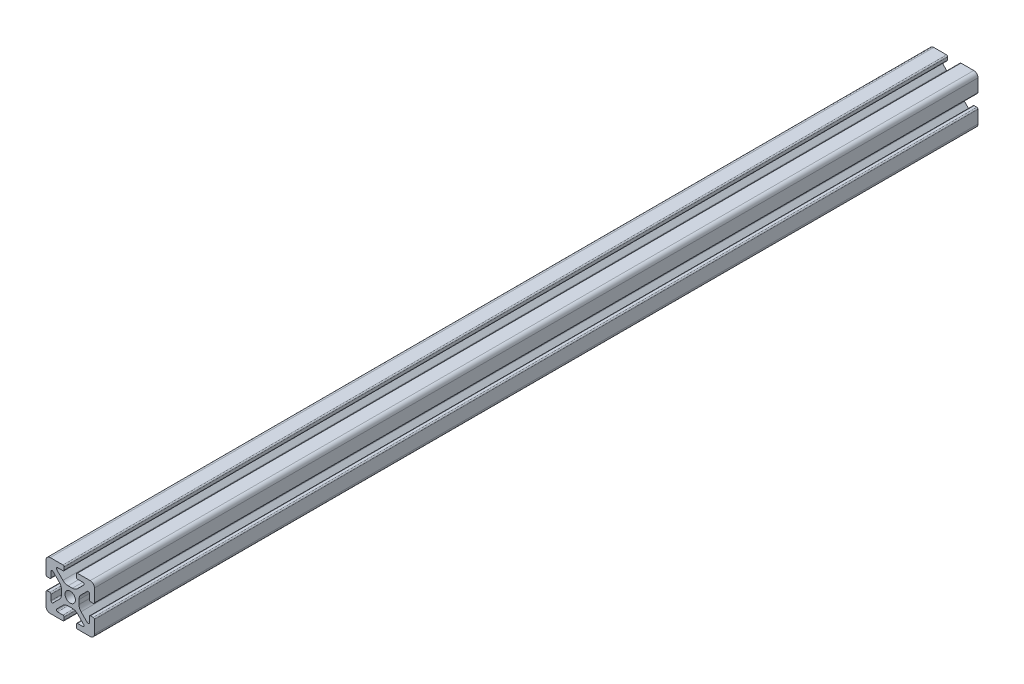
SolidWorks part; units mm, degrees
ref_plane "Front Plane" through (0, 0, 0) normal (0, 0, 1) x (1, 0, 0)
ref_plane "Top Plane" through (0, 0, 0) normal (0, 1, 0) x (1, 0, 0)
ref_plane "Right Plane" through (0, 0, 0) normal (1, 0, 0) x (0, 0, -1)
sketch "Sketch2" plane through (0, 0, 0) normal (0, 0, 1) x (1, 0, 0)
  line L0 (0, 10) -> (0, -10) construction
  line L1 (-10, 0) -> (10, 0) construction
  line L2 (2.5, -10) -> (10, -10)
  line L3 (10, -10) -> (10, -2.5)
  line L4 (2.5, -10) -> (2.5, -7.9246)
  line L5 (2.5, -7.9246) -> (6.4571, -7.9246)
  line L6 (6.4571, -7.9246) -> (2.1325, -3.6)
  line L7 (0, 0) -> (10, -10) construction
  line L8 (10, -2.5) -> (7.9246, -2.5)
  line L9 (7.9246, -2.5) -> (7.9246, -6.4571)
  line L10 (7.9246, -6.4571) -> (3.6, -2.1325)
  line L11 (5.7623, -4.2948) -> (4.2948, -5.7623) construction
  circle A0 centre (0, 0) radius 2.15
  arc A1 (5.25, -7.9246) -> (5.6036, -7.0711) centre (5.25, -7.4246) ccw construction
  point P8 (0, -3.6)
  point P16 (5.0286, -5.0286)
  dimension "Center Hole Diameter" = 4.3
  dimension "D3" = 0.5
  dimension "Rail Height" = 20
  dimension "Rail Width" = 20
  dimension "T-Slot Width" = 5
  dimension "Slot Depth" = 6.4
  dimension "Slot Inner Width" = 11.5
sketch "Sketch3" plane through (0, 0, 0) normal (1, 0, 0) x (0, 0, -1)
  line L0 (-182.5, -10) -> (182.5, -10) construction
  line L1 (-157.1, 0) -> (157.1, 0) construction
  dimension "Length" = 365
  dimension "D1" = 25.4
sketch "Sketch4" plane through (0, 0, 0) normal (0, 0, 1) x (1, 0, 0)
  line L0 (3, -10) -> (8.25, -10)
  line L1 (2.5, -10) -> (10, -10) construction
  line L2 (2.5, -10) -> (2.5, -7.9246) construction
  line L3 (2.5, -7.9246) -> (6.4571, -7.9246) construction
  line L4 (2.5, -8.4246) -> (2.5, -9.5)
  line L5 (3, -7.9246) -> (5.25, -7.9246)
  line L6 (0, -3.6) -> (0.8898, -3.6)
  line L7 (6.4571, -7.9246) -> (2.1325, -3.6) construction
  line L8 (3.0112, -4.4787) -> (5.6036, -7.0711)
  line L9 (10, -10) -> (10, -2.5) construction
  line L10 (7.9246, -6.4571) -> (3.6, -2.1325) construction
  line L11 (7.9246, -2.5) -> (7.9246, -6.4571) construction
  line L12 (7.9246, -5.25) -> (7.9246, -3)
  line L13 (10, -2.5) -> (7.9246, -2.5) construction
  line L14 (8.4246, -2.5) -> (9.5, -2.5)
  line L15 (10, -3) -> (10, -8.25)
  line L16 (7.0711, -5.6036) -> (4.4787, -3.0112)
  line L17 (3.6, 0) -> (3.6, -0.8898)
  line L18 (-10, 0) -> (10, 0) construction
  line L19 (0, -3.6) -> (0, -2.15)
  line L20 (0, 10) -> (0, -10) construction
  line L21 (3.6, 0) -> (2.15, 0)
  arc A0 (2.5, -9.5) -> (3, -10) centre (3, -9.5) ccw
  arc A1 (5.25, -7.9246) -> (5.6036, -7.0711) centre (5.25, -7.4246) ccw construction
  arc A2 (2.5, -8.4246) -> (3, -7.9246) centre (3, -8.4246) cw
  arc A3 (5.25, -7.9246) -> (5.6036, -7.0711) centre (5.25, -7.4246) ccw
  arc A4 (0.8898, -3.6) -> (3.0112, -4.4787) centre (0.8898, -6.6) cw
  arc A5 (8.25, -10) -> (10, -8.25) centre (8.25, -8.25) ccw
  arc A6 (7.0711, -5.6036) -> (7.9246, -5.25) centre (7.4246, -5.25) ccw
  arc A7 (7.9246, -3) -> (8.4246, -2.5) centre (8.4246, -3) cw
  arc A8 (9.5, -2.5) -> (10, -3) centre (9.5, -3) cw
  arc A9 (4.4787, -3.0112) -> (3.6, -0.8898) centre (6.6, -0.8898) cw
  circle A10 centre (0, 0) radius 2.15 construction
  arc A11 (0, -2.15) -> (2.15, 0) centre (0, 0) ccw
  dimension "D1" = 1.75
  dimension "D2" = 3
extrude "Boss-Extrude1" add sketch "Sketch4" along normal mid plane 365
mirror "Mirror1" about plane through (0, 0, 0) normal (1, 0, 0) of bodies 134
mirror "Mirror2" about plane through (0, 0, 0) normal (0, 1, 0) of bodies 135
equation "\"D3@Sketch2\"=\"T-Slot Width@Sketch2\"*0.1"
equation "\"D1@Sketch4\"=\"D3@Sketch2\"*3.5"
equation "\"D2@Sketch4\"=\"D3@Sketch2\"*6"
equation "\"D1@Boss-Extrude1\"= \"Length@Sketch3\""
equation "\"Length\"= 365mm"
equation "\"Length@Sketch3\"=\"Length\""
